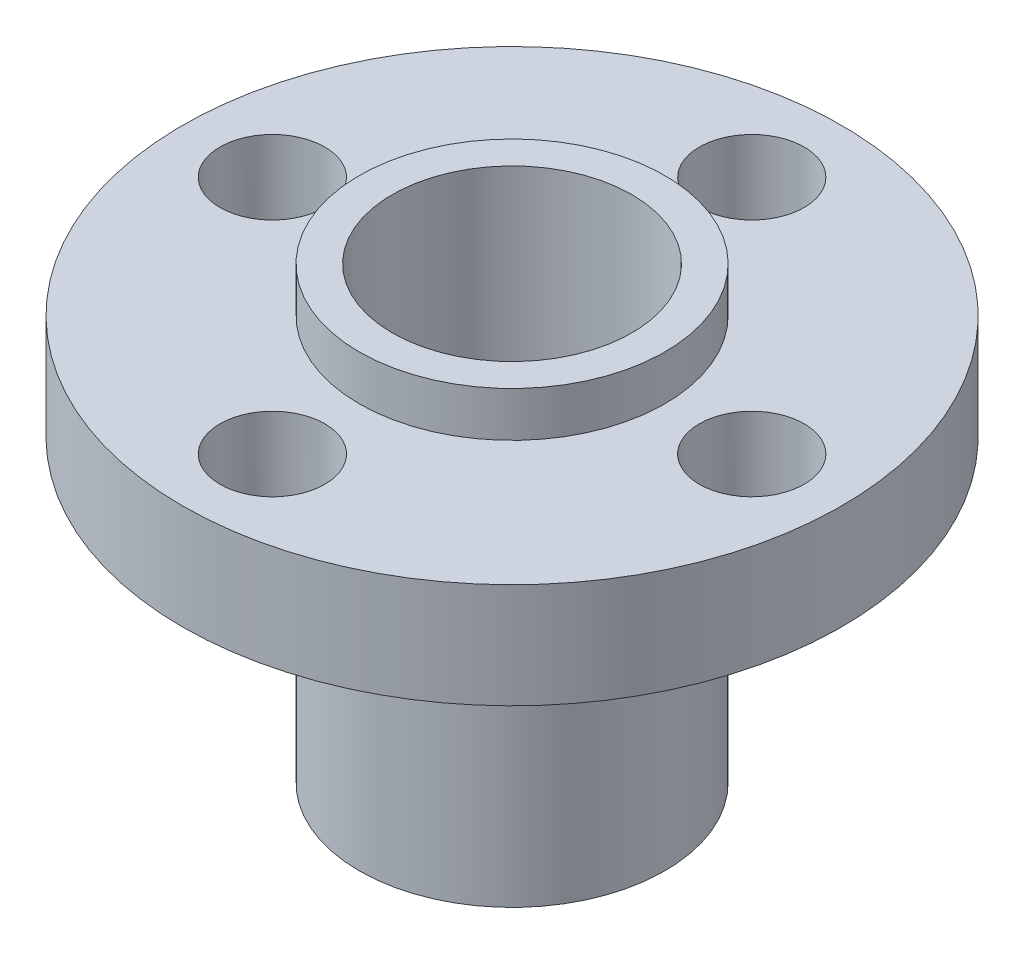
SolidWorks part; units mm, degrees
ref_plane "Plano frontal" through (0, 0, 0) normal (0, 0, 1) x (1, 0, 0)
ref_plane "Plano superior" through (0, 0, 0) normal (0, 1, 0) x (1, 0, 0)
ref_plane "Plano direito" through (0, 0, 0) normal (1, 0, 0) x (0, 0, -1)
sketch "Esboço1" plane through (0, 0, 0) normal (0, 1, 0) x (1, 0, 0)
  circle A0 centre (0, 0) radius 11
  dimension "D1" = 22
extrude "Ressalto-extrusão1" add sketch "Esboço1" along normal blind 3.5
sketch "Esboço2" plane through (0, 3.5, 0) normal (0, 1, 0) x (1, 0, 0)
  circle A0 centre (0, 0) radius 5.1
  dimension "D1" = 10.2
extrude "Ressalto-extrusão2" add sketch "Esboço2" along normal blind 1.5 and the other way blind 13.5
sketch "Esboço3" plane through (0, 5, 0) normal (0, 1, 0) x (1, 0, 0)
  circle A0 centre (0, 0) radius 4
  dimension "D1" = 8
extrude "Corte-extrusão1" cut sketch "Esboço3" against normal through all
sketch "Esboço4" plane through (0, 3.5, 0) normal (0, 1, 0) x (1, 0, 0)
  circle A0 centre (0, 8) radius 1.75
  dimension "D1" = 3.5
  dimension "D2" = 8
extrude "Corte-extrusão2" cut sketch "Esboço4" against normal through all
pattern_circular "PadrãoCircular1" count 4 every 90 about axis through (0, 0, 0) along (0, 1, 0) of "Corte-extrusão2"
